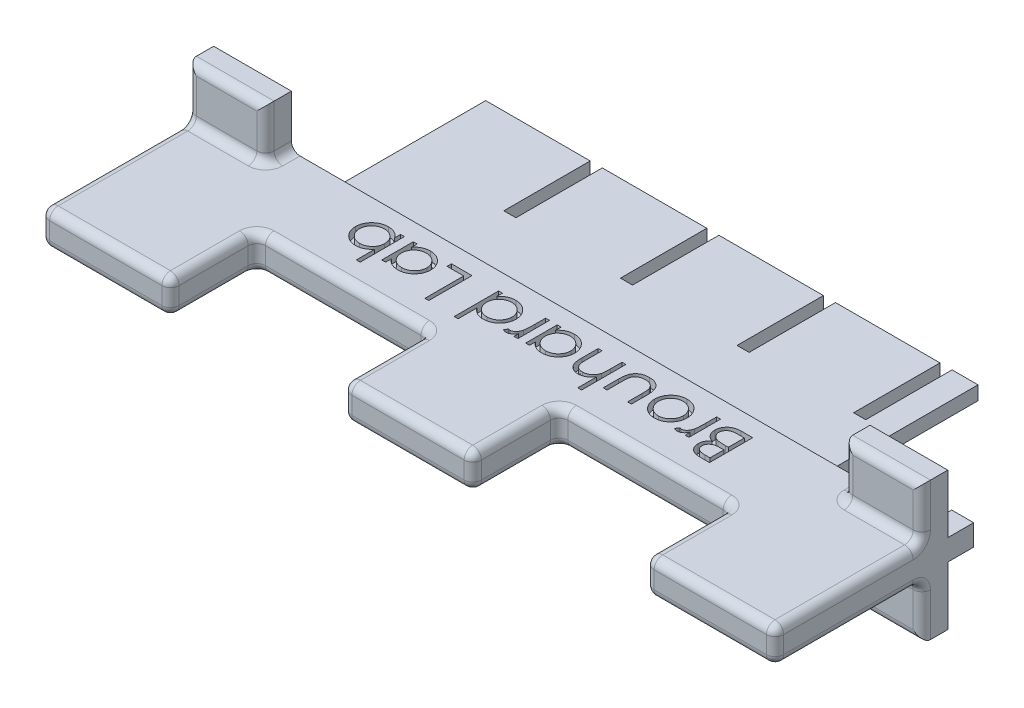
SolidWorks part; units mm, degrees
ref_plane "Front Plane" through (0, 0, 0) normal (0, 0, 1) x (1, 0, 0)
ref_plane "Top Plane" through (0, 0, 0) normal (0, 1, 0) x (1, 0, 0)
ref_plane "Right Plane" through (0, 0, 0) normal (1, 0, 0) x (0, 0, -1)
sketch "Sketch1" plane through (0, 0, 0) normal (0, 0, 1) x (1, 0, 0)
  line L1 (-42.5, 2) -> (42.5, 2)
  line L2 (-42.5, 2) -> (-42.5, -2)
  line L3 (-42.5, -2) -> (42.5, -2)
  line L4 (42.5, 2) -> (42.5, -2)
  line L5 (-42.5, 2) -> (42.5, -2) construction
  line L6 (-42.5, -2) -> (42.5, 2) construction
  point P0 (0, 0)
  dimension "D1" = 85
  dimension "D2" = 4
extrude "Boss-Extrude1" add sketch "Sketch1" along normal blind 10
sketch "Sketch2" plane through (0, 0, 10) normal (0, 0, 1) x (1, 0, 0)
  line L0 (-42.5, -2) -> (42.5, -2) construction
  line L1 (-42.5, 2) -> (-27.5, 2)
  line L2 (-42.5, 2) -> (-42.5, -2)
  line L3 (-42.5, -2) -> (-27.5, -2)
  line L4 (-27.5, 2) -> (-27.5, -2)
  line L6 (42.5, 2) -> (27.5, 2)
  line L7 (42.5, 2) -> (42.5, -2)
  line L8 (42.5, -2) -> (27.5, -2)
  line L9 (27.5, 2) -> (27.5, -2)
  line L10 (-7.5, 2) -> (7.5, 2)
  line L11 (-7.5, 2) -> (-7.5, -2)
  line L12 (-7.5, -2) -> (7.5, -2)
  line L13 (7.5, 2) -> (7.5, -2)
  line L14 (-7.5, 2) -> (7.5, -2) construction
  line L15 (-7.5, -2) -> (7.5, 2) construction
  point P12 (0, 0)
  dimension "D1" = 15
extrude "Boss-Extrude2" add sketch "Sketch2" along normal blind 10
sketch "Sketch3" plane through (0, 0, 0) normal (0, 0, -1) x (-1, 0, 0)
  line L9 (42.5, -1.225) -> (39.95, -1.225)
  line L10 (42.5, -1.225) -> (42.5, 1.225)
  line L11 (42.5, 1.225) -> (39.95, 1.225)
  line L12 (39.95, -1.225) -> (39.95, 1.225)
  line L13 (42.5, -1.225) -> (39.95, 1.225) construction
  line L14 (42.5, 1.225) -> (39.95, -1.225) construction
  line L15 (42.5, 2) -> (42.5, -2) construction
  line L16 (0, 0) -> (0, 13.9589)
  line L17 (-42.5, 1.225) -> (-39.95, -1.225) construction
  line L18 (-42.5, -1.225) -> (-39.95, 1.225) construction
  line L19 (-39.95, -1.225) -> (-39.95, 1.225)
  line L20 (-42.5, 1.225) -> (-39.95, 1.225)
  line L21 (-42.5, -1.225) -> (-42.5, 1.225)
  line L22 (-42.5, -1.225) -> (-39.95, -1.225)
  point P3 (42.5, 0)
  point P10 (41.225, 0)
  point P16 (-41.225, 0)
  line M3 (-42.5, 2) -> (-42.5, -2)
  dimension "D1" = 2.45
  dimension "D2" = 2.55
extrude "Boss-Extrude3" add sketch "Sketch3" along normal blind 3 contours L22 L19 L20 M3 | L12 L11 L10 L9
sketch "Sketch4" plane through (0, 0, 0) normal (0, 0, -1) x (-1, 0, 0)
  line L1 (28.5, -0.8) -> (-28.5, -0.8)
  line L2 (28.5, -0.8) -> (28.5, 0.8)
  line L3 (28.5, 0.8) -> (-28.5, 0.8)
  line L4 (-28.5, -0.8) -> (-28.5, 0.8)
  line L5 (28.5, -0.8) -> (-28.5, 0.8) construction
  line L6 (28.5, 0.8) -> (-28.5, -0.8) construction
  point P0 (0, 0)
  dimension "D1" = 1.6
  dimension "D2" = 57
extrude "Boss-Extrude4" add sketch "Sketch4" along normal blind 7.5
sketch "Sketch6" plane through (0, 0, 0) normal (0, 0, -1) x (-1, 0, 0)
  line L1 (42.5, -2) -> (33.5, -2)
  line L2 (42.5, -2) -> (42.5, -8)
  line L3 (42.5, -8) -> (33.5, -8)
  line L4 (33.5, -2) -> (33.5, -8)
  line L5 (42.5, 2) -> (33.5, 2)
  line L6 (42.5, 2) -> (42.5, 8)
  line L7 (42.5, 8) -> (33.5, 8)
  line L8 (33.5, 2) -> (33.5, 8)
  line L9 (-42.5, -2) -> (-33.5, -2)
  line L10 (-42.5, -2) -> (-42.5, -8)
  line L11 (-42.5, -8) -> (-33.5, -8)
  line L12 (-33.5, -2) -> (-33.5, -8)
  line L13 (-42.5, 2) -> (-33.5, 2)
  line L14 (-42.5, 2) -> (-42.5, 8)
  line L15 (-42.5, 8) -> (-33.5, 8)
  line L16 (-33.5, 2) -> (-33.5, 8)
  dimension "D1" = 6
  dimension "D2" = 9
extrude "Boss-Extrude6" add sketch "Sketch6" against normal blind 3
fillet "Fillet1" radius 1 52 edges at (-42.5, -2, 11.5) (-33.5, -2, 1.5) (-38, -2, 3) (-33.5, -5, 3) (-38, -8, 3) (-42.5, -5, 3) (-27.5, 0, 20) (-35, -2, 20) (-42.5, 0, 20) (-35, 2, 20) (33.5, -2, 1.5) (42.5, -2, 11.5) (42.5, 2, 11.5) (33.5, 2, 1.5) (-33.5, 2, 1.5) (-42.5, 2, 11.5) (38, -8, 3) (33.5, -5, 3) (38, -2, 3) (42.5, -5, 3) (35, -2, 20) (27.5, 0, 20) (35, 2, 20) (42.5, 0, 20) (38, 2, 3) (33.5, 5, 3) (38, 8, 3) (42.5, 5, 3) (0, -2, 20) (-7.5, 0, 20) (0, 2, 20) (7.5, 0, 20) (-38, 8, 3) (-33.5, 5, 3) (-38, 2, 3) (-42.5, 5, 3) (27.5, 2, 15) (27.5, -2, 15) (27.5, 0, 10) (17.5, -2, 10) (17.5, 2, 10) (7.5, -2, 15) (7.5, 2, 15) (7.5, 0, 10) (-7.5, 2, 15) (-7.5, -2, 15) (-27.5, -2, 15) (-27.5, 2, 15) (-27.5, 0, 10) (-17.5, 2, 10) (-7.5, 0, 10) (-17.5, -2, 10)
ref_plane "Plane1" through (0, 0, 0) normal (0, 1, 0) x (1, 0, 0)
sketch "Sketch7" plane through (0, 2, 0) normal (0, 1, 0) x (1, 0, 0)
  line L0 (30.9142, -2.045) -> (-30.9142, -2.045)
  line L1 (32.5, 0) -> (-32.5, 0) construction
  point P2 (0, -2.045)
  point P5 (0, 0)
sketch "Sketch8" plane through (0, 2, 0) normal (0, 1, 0) x (1, 0, 0)
  text T0 "Brouhard Lab" font "Century Gothic" height 5
extrude "Cut-Extrude1" cut sketch "Sketch8" against normal blind 1
sketch "Sketch5" plane through (0, 0, -7.5) normal (0, 0, -1) x (-1, 0, 0)
  line L0 (28.5, 0.8) -> (-28.5, 0.8) construction
  line L1 (28.5, -0.8) -> (16.4, -0.8)
  line L2 (28.5, -0.8) -> (28.5, 0.8)
  line L3 (28.5, 0.8) -> (16.4, 0.8)
  line L4 (16.4, -0.8) -> (16.4, 0.8)
  line L97 (15, -0.8) -> (2.9, -0.8)
  line L98 (15, -0.8) -> (15, 0.8)
  line L99 (15, 0.8) -> (2.9, 0.8)
  line L100 (2.9, -0.8) -> (2.9, 0.8)
  line L101 (1.5, -0.8) -> (-10.6, -0.8)
  line L102 (1.5, -0.8) -> (1.5, 0.8)
  line L103 (1.5, 0.8) -> (-10.6, 0.8)
  line L104 (-10.6, -0.8) -> (-10.6, 0.8)
  line L105 (-12, -0.8) -> (-24.1, -0.8)
  line L106 (-12, -0.8) -> (-12, 0.8)
  line L107 (-12, 0.8) -> (-24.1, 0.8)
  line L108 (-24.1, -0.8) -> (-24.1, 0.8)
  line L154 (-28.5, -0.8) -> (-25.5, -0.8)
  line L155 (-28.5, -0.8) -> (-28.5, 0.8)
  line L156 (-28.5, 0.8) -> (-25.5, 0.8)
  line L157 (-25.5, -0.8) -> (-25.5, 0.8)
  dimension "D2" = 12.1
  dimension "D3" = 3
  dimension "D1" = 4
extrude "Boss-Extrude5" add sketch "Sketch5" along normal blind 10
